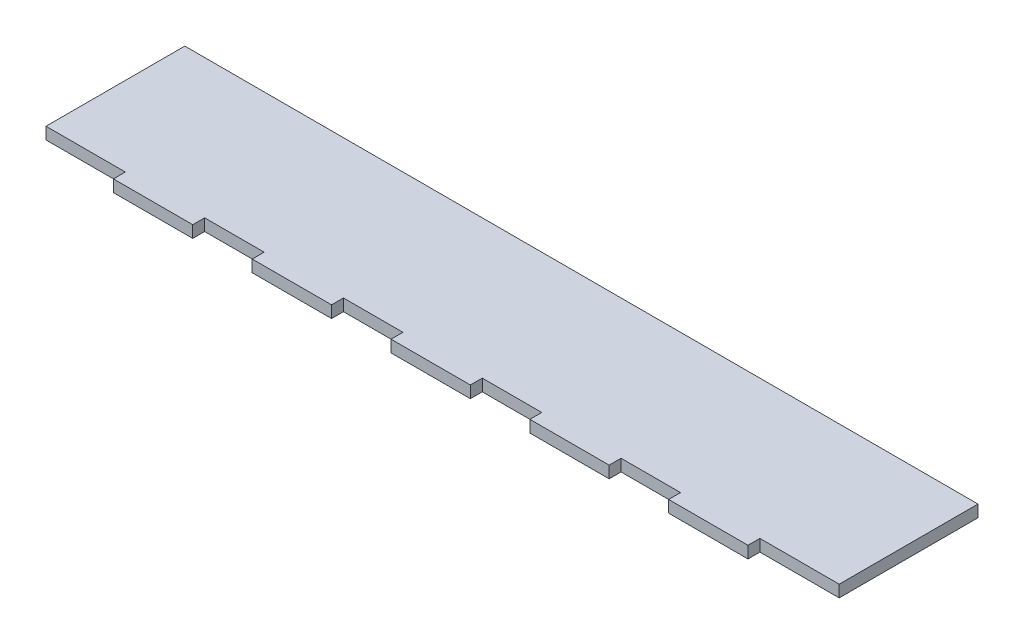
SolidWorks part; units mm, degrees
ref_plane "Front Plane" through (0, 0, 0) normal (0, 0, 1) x (1, 0, 0)
ref_plane "Top Plane" through (0, 0, 0) normal (0, 1, 0) x (1, 0, 0)
ref_plane "Right Plane" through (0, 0, 0) normal (1, 0, 0) x (0, 0, -1)
sketch "Sketch1" plane through (0, 0, 0) normal (0, 1, 0) x (1, 0, 0)
  line L0 (40, 0) -> (55, 0)
  line L1 (0, 0) -> (20, 0)
  line L2 (0, 0) -> (0, 35)
  line L3 (0, 35) -> (200, 35)
  line L4 (200, 0) -> (200, 35)
  line L5 (0, 0) -> (200, 35) construction
  line L6 (0, 35) -> (200, 0) construction
  line L7 (55, -3) -> (75, -3)
  line L8 (20, 0) -> (20, -3)
  line L9 (20, -3) -> (40, -3)
  line L10 (40, 0) -> (40, -3)
  line L11 (75, 0) -> (75, -3)
  line L12 (55, 0) -> (55, -3)
  line L13 (90, -3) -> (110, -3)
  line L14 (110, 0) -> (110, -3)
  line L15 (90, 0) -> (90, -3)
  line L16 (125, -3) -> (145, -3)
  line L17 (145, 0) -> (145, -3)
  line L18 (125, 0) -> (125, -3)
  line L19 (160, -3) -> (180, -3)
  line L20 (180, 0) -> (180, -3)
  line L21 (160, 0) -> (160, -3)
  line L22 (75, 0) -> (90, 0)
  line L23 (110, 0) -> (125, 0)
  line L24 (145, 0) -> (160, 0)
  line L25 (180, 0) -> (200, 0)
  point P4 (100, 17.5)
  point P10 (25.3866, 2.1907)
  dimension "D1" = 20
  dimension "D2" = 20
  dimension "D3" = 3
  dimension "D4" = 200
  dimension "D5" = 35
  dimension "D7" = 15
  dimension "D6" = 5
extrude "Boss-Extrude1" add sketch "Sketch1" along normal blind 3 contours L3 L4 L25 L20 L19 L21 L24 L17 L16 L18 L23 L14 L13 L15 L22 L11 L7 L12 L0 L10 L9 L8 L1 L2
